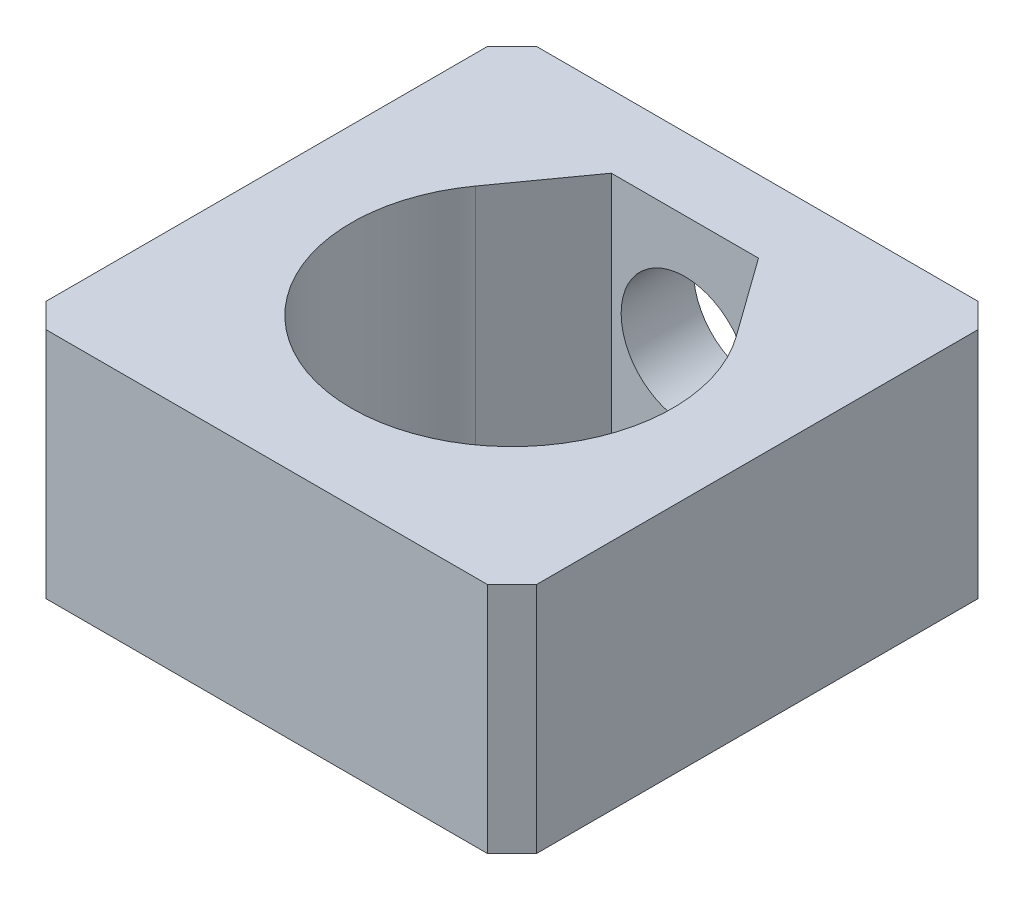
SolidWorks part; units mm, degrees
ref_plane "Front Plane" through (0, 0, 0) normal (0, 0, 1) x (1, 0, 0)
ref_plane "Top Plane" through (0, 0, 0) normal (0, 1, 0) x (1, 0, 0)
ref_plane "Right Plane" through (0, 0, 0) normal (1, 0, 0) x (0, 0, -1)
sketch "Sketch1" plane through (0, 0, 0) normal (0, 1, 0) x (1, 0, 0)
  line L0 (-5.3194, 3.8219) -> (-3, 7.05)
  line L1 (-3, 7.05) -> (3, 7.05)
  line L2 (3, 7.05) -> (5.3194, 3.8219)
  line L3 (0, 7.05) -> (0, 0) construction
  line L4 (0, 0) -> (0, -6.55) construction
  line L6 (-10, 10) -> (10, 10)
  line L7 (-10, 10) -> (-10, -10)
  line L8 (-10, -10) -> (10, -10)
  line L9 (10, 10) -> (10, -10)
  line L10 (-10, 10) -> (10, -10) construction
  line L11 (-10, -10) -> (10, 10) construction
  arc A0 (-5.3194, 3.8219) -> (5.3194, 3.8219) centre (0, 0) ccw
  arc A1 (0, 6.55) -> (-5.3194, 3.8219) centre (0, 0) ccw construction
  arc A2 (5.3194, 3.8219) -> (0, 6.55) centre (0, 0) ccw construction
  point P13 (0, 0)
  dimension "D1" = 13.1
  dimension "D2" = 13.6
  dimension "D3" = 6
  dimension "D4" = 20
extrude "Boss-Extrude1" add sketch "Sketch1" along normal blind 9.5
sketch "Sketch3" plane through (0, 0, -10) normal (0, 0, -1) x (-1, 0, 0)
  line L0 (0, 0) -> (0, 9.5) construction
  line L1 (-10, 0) -> (10, 0) construction
  line L2 (-10, 9.5) -> (10, 9.5) construction
  circle A0 centre (0, 4.75) radius 2.6
  dimension "D1" = 5.2
extrude "Cut-Extrude1" cut sketch "Sketch3" against normal up to next
chamfer "Chamfer1" distance 1 angle 45 4 edges at (-10, 4.75, 10) (-10, 4.75, -10) (10, 4.75, -10) (10, 4.75, 10)
